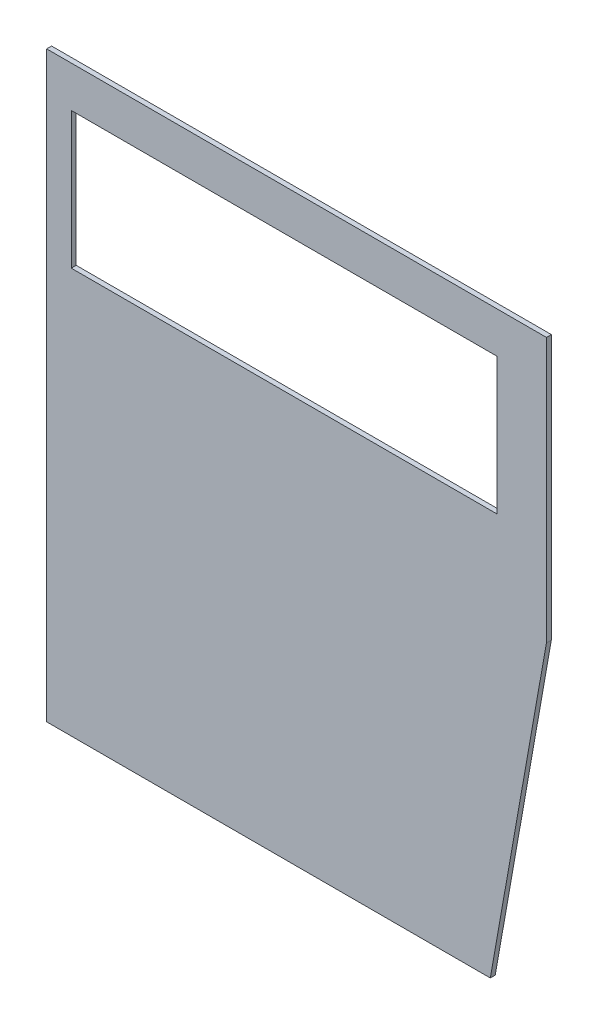
SolidWorks part; units mm, degrees
material "AISI 316 Stainless Steel Sheet (SS)"
ref_plane "Front Plane" through (0, 0, 0) normal (0, 0, 1) x (1, 0, 0)
ref_plane "Top Plane" through (0, 0, 0) normal (0, 1, 0) x (1, 0, 0)
ref_plane "Right Plane" through (0, 0, 0) normal (1, 0, 0) x (0, 0, -1)
sketch "Sketch1" plane through (0, 0, 0) normal (0, 0, 1) x (1, 0, 0)
  line L0 (816.1767, 30) -> (1086.3949, 30) construction
  line L1 (1086.3949, 30) -> (1120.5748, 223.8439) construction
  line L2 (1120.5748, 223.8439) -> (1120.5748, 385) construction
  line L3 (1120.5748, 385) -> (816.1767, 385) construction
  line L4 (816.1767, 385) -> (816.1767, 30) construction
  line L5 (816.1767, 30) -> (1086.3949, 30)
  line L6 (1086.3949, 30) -> (1120.5748, 223.8439)
  line L7 (1120.5748, 223.8439) -> (1120.5748, 385)
  line L8 (1120.5748, 385) -> (816.1767, 385)
  line L9 (816.1767, 385) -> (816.1767, 30)
  line L10 (831.1767, 360) -> (1090.5748, 360)
  line L11 (1090.5748, 360) -> (1090.5748, 276.8092)
  line L12 (1090.5748, 276.8092) -> (831.1767, 276.8092)
  line L13 (831.1767, 276.8092) -> (831.1767, 360)
  line L14 (711.1767, 276.8092) -> (711.1767, 360) construction
  line L15 (711.1767, 360) -> (499.6574, 360) construction
  dimension "D1" = 15
  dimension "D2" = 30
extrude "Boss-Extrude1" add sketch "Sketch1" against normal blind 3
